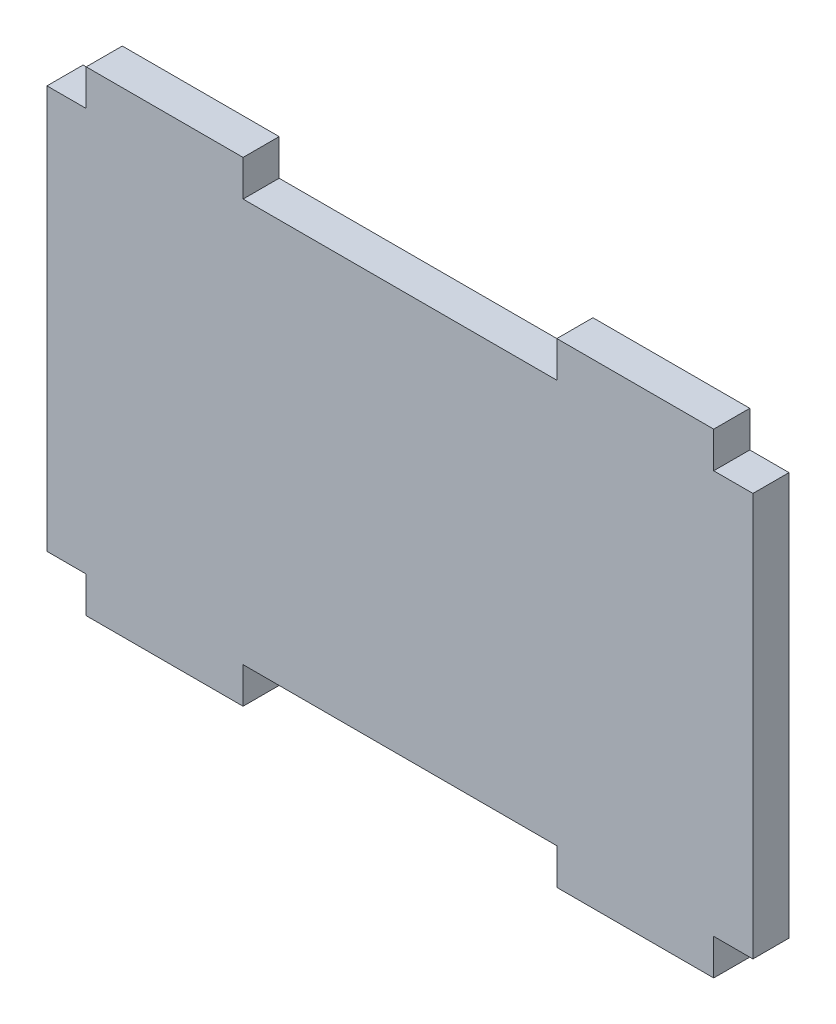
SolidWorks part; units mm, degrees
ref_plane "Front Plane" through (0, 0, 0) normal (0, 0, 1) x (1, 0, 0)
ref_plane "Top Plane" through (0, 0, 0) normal (0, 1, 0) x (1, 0, 0)
ref_plane "Right Plane" through (0, 0, 0) normal (1, 0, 0) x (0, 0, -1)
ref_plane "Plane1" through (0, 0, 2.9972) normal (0, 0, 1) x (1, 0, 0)
sketch "Sketch1" plane through (0, 0, 2.9972) normal (0, 0, 1) x (1, 0, 0)
  line L0 (0, 0) -> (0, 2.3) construction
  line L1 (0, 2.3) -> (0, 28)
  line L2 (0, 28) -> (0, 30.3) construction
  line L3 (0, 0) -> (45, 0) construction
  line L4 (0, 30.3) -> (45, 30.3) construction
  line L5 (45, 30.3) -> (45, 0) construction
  line L6 (0, 28) -> (45, 28) construction
  line L7 (0, 2.3) -> (45, 2.3) construction
  line L8 (22.5, 2.3) -> (12.5, 2.3)
  line L9 (22.5, 2.3) -> (32.5, 2.3)
  line L10 (12.5, 2.3) -> (12.5, 28) construction
  line L11 (32.5, 2.3) -> (32.5, 28) construction
  line L12 (12.5, 28) -> (32.5, 28)
  line L13 (12.5, 2.3) -> (12.5, 0)
  line L14 (12.5, 0) -> (2.5, 0)
  line L15 (32.5, 2.3) -> (32.5, 0)
  line L16 (32.5, 0) -> (42.5, 0)
  line L17 (2.5, 0) -> (2.5, 2.3)
  line L18 (2.5, 2.3) -> (0, 2.3)
  line L19 (42.5, 0) -> (42.5, 2.3)
  line L20 (42.5, 2.3) -> (45, 2.3)
  line L21 (45, 2.3) -> (45, 28)
  line L22 (2.5, 2.3) -> (2.5, 30.3) construction
  line L23 (42.5, 2.3) -> (42.5, 30.3) construction
  line L24 (0, 28) -> (2.5, 28)
  line L25 (2.5, 28) -> (2.5, 30.3)
  line L26 (2.5, 30.3) -> (12.5, 30.3)
  line L27 (12.5, 30.3) -> (12.5, 28)
  line L28 (32.5, 28) -> (32.5, 30.3)
  line L29 (32.5, 30.3) -> (42.5, 30.3)
  line L30 (42.5, 30.3) -> (42.5, 28)
  line L31 (42.5, 28) -> (45, 28)
  dimension "D1" = 2.3
  dimension "D2" = 25.7
  dimension "D3" = 2.3
  dimension "D4" = 45
  dimension "D5" = 10
  dimension "D6" = 10
  dimension "D7" = 10
  dimension "D8" = 10
extrude "Boss-Extrude1" add sketch "Sketch1" against normal blind 2.3
